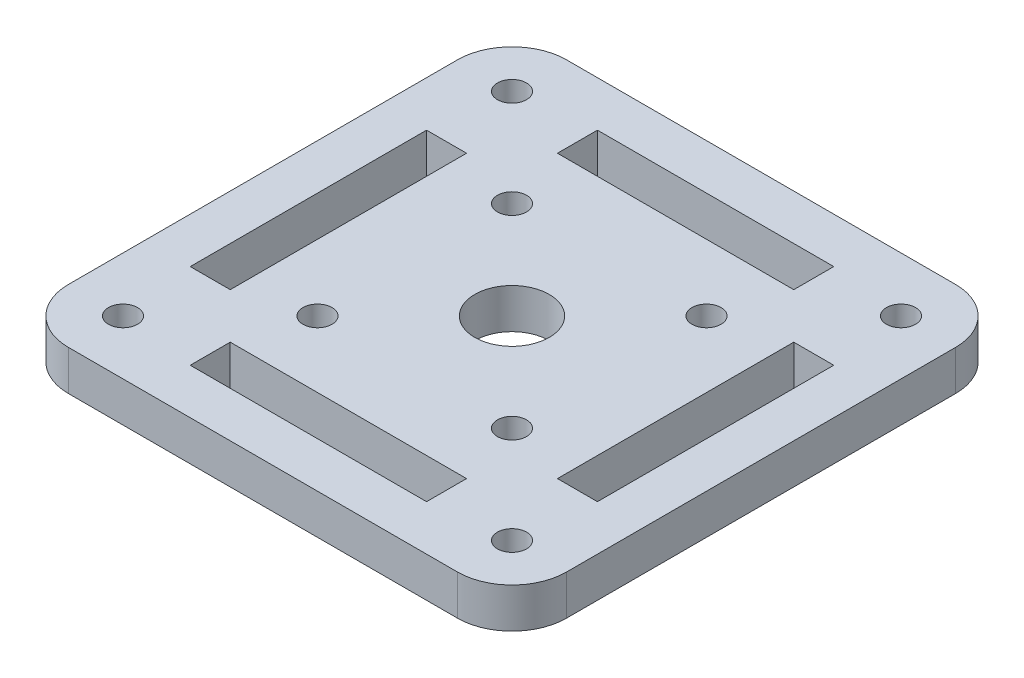
SolidWorks part; units mm, degrees
ref_plane "前视基准面" through (0, 0, 0) normal (0, 0, 1) x (1, 0, 0)
ref_plane "上视基准面" through (0, 0, 0) normal (0, 1, 0) x (1, 0, 0)
ref_plane "右视基准面" through (0, 0, 0) normal (1, 0, 0) x (0, 0, -1)
sketch "草图1" plane through (0, 0, 0) normal (0, 1, 0) x (1, 0, 0)
  line L0 (0, 0) -> (27.4, 27.4) construction
  line L1 (-27.4, 27.4) -> (27.4, 27.4)
  line L2 (-27.4, 27.4) -> (-27.4, -27.4)
  line L3 (-27.4, -27.4) -> (27.4, -27.4)
  line L4 (27.4, 27.4) -> (27.4, -27.4)
  line L5 (0, -27.4) -> (0, 27.4) construction
  line L6 (-27.4, 0) -> (27.4, 0) construction
  line L7 (18, -5) -> (18, 5)
  line L8 (18, 5) -> (22.4, 5) construction
  line L9 (22.4, 5) -> (22.4, -5)
  line L10 (18, 5) -> (18, 13)
  line L11 (18, 13) -> (22.4, 13)
  line L12 (22.4, 13) -> (22.4, 5)
  line L13 (0, 0) -> (27.4, -27.4) construction
  line L14 (22.4, -13) -> (22.4, -5)
  line L15 (18, -13) -> (22.4, -13)
  line L16 (18, -5) -> (18, -13)
  line L17 (18, -5) -> (22.4, -5) construction
  line L18 (-5, 18) -> (-5, 22.4) construction
  line L19 (5, 18) -> (5, 22.4) construction
  line L20 (-5, 18) -> (-13, 18)
  line L21 (-13, 18) -> (-13, 22.4)
  line L22 (-13, 22.4) -> (-5, 22.4)
  line L23 (13, 22.4) -> (5, 22.4)
  line L24 (13, 18) -> (13, 22.4)
  line L25 (5, 18) -> (13, 18)
  line L26 (5, 22.4) -> (-5, 22.4)
  line L27 (-5, 18) -> (5, 18)
  line L28 (0, 0) -> (-27.4, -27.4) construction
  line L29 (0, 0) -> (-27.4, 27.4) construction
  line L30 (5, -18) -> (5, -22.4) construction
  line L31 (-5, -18) -> (-5, -22.4) construction
  line L32 (5, -18) -> (13, -18)
  line L33 (13, -18) -> (13, -22.4)
  line L34 (13, -22.4) -> (5, -22.4)
  line L35 (-13, -22.4) -> (-5, -22.4)
  line L36 (-13, -18) -> (-13, -22.4)
  line L37 (-5, -18) -> (-13, -18)
  line L38 (-5, -22.4) -> (5, -22.4)
  line L39 (5, -18) -> (-5, -18)
  line L40 (-18, -5) -> (-22.4, -5) construction
  line L41 (-18, 5) -> (-22.4, 5) construction
  line L42 (-18, 5) -> (-18, -5)
  line L43 (-22.4, -5) -> (-22.4, 5)
  line L44 (-18, -5) -> (-18, -13)
  line L45 (-18, -13) -> (-22.4, -13)
  line L46 (18, 13) -> (18, 18) construction
  line L47 (-22.4, -13) -> (-22.4, -5)
  line L48 (-22.4, 13) -> (-22.4, 5)
  line L49 (-18, 13) -> (-22.4, 13)
  line L50 (-18, 5) -> (-18, 13)
  circle A0 centre (0, 0) radius 4.1
  circle A1 centre (21.4, 21.4) radius 1.6
  circle A2 centre (21.4, -21.4) radius 1.6
  circle A3 centre (-21.4, -21.4) radius 1.6
  circle A4 centre (-21.4, 21.4) radius 1.6
  point P17 (22.4, 0)
  point P18 (18, 0)
  point P32 (0, 18)
  point P33 (0, 22.4)
  point P42 (0, -18)
  point P43 (0, -22.4)
  point P53 (-22.4, 0)
  point P54 (-18, 0)
  dimension "D1" = 8.2
  dimension "D8" = 3.2
  dimension "D2" = 45
  dimension "D3" = 4.4
  dimension "D5" = 5
  dimension "D6" = 8
  dimension "D7" = 5
  dimension "D9" = 6
extrude "凸台-拉伸1" add sketch "草图1" along normal blind 4.4
fillet "圆角1" radius 6 4 edges at (-27.4, 2.2, 27.4) (-27.4, 2.2, -27.4) (27.4, 2.2, -27.4) (27.4, 2.2, 27.4)
sketch "草图2" plane through (0, 4.4, 0) normal (0, 1, 0) x (1, 0, 0)
  line L0 (0, 0) -> (21.4, 21.4) construction
  circle A0 centre (10.7, 10.7) radius 1.6
  circle A1 centre (10.7, -10.7) radius 1.6
  circle A2 centre (-10.7, -10.7) radius 1.6
  circle A3 centre (-10.7, 10.7) radius 1.6
  point P15 (0, 0)
  dimension "D1" = 3.2
  dimension "D2" = 4
extrude "切除-拉伸1" cut sketch "草图2" against normal blind 10
